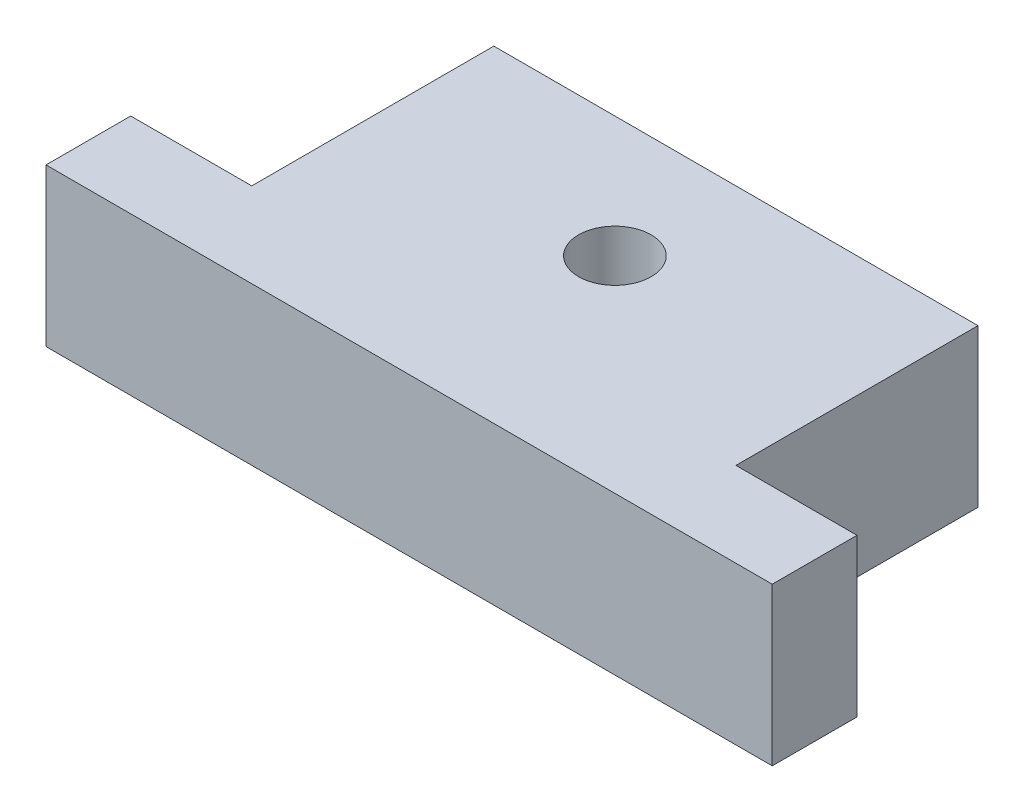
SolidWorks part; units mm, degrees
ref_plane "Front Plane" through (0, 0, 0) normal (0, 0, 1) x (1, 0, 0)
ref_plane "Top Plane" through (0, 0, 0) normal (0, 1, 0) x (1, 0, 0)
ref_plane "Right Plane" through (0, 0, 0) normal (1, 0, 0) x (0, 0, -1)
sketch "Sketch1" plane through (0, 0, 0) normal (0, 1, 0) x (1, 0, 0)
  line L0 (-23.4364, 11.7908) -> (36.5636, 11.7908)
  line L1 (36.5636, 11.7908) -> (36.5636, 18.7908)
  line L2 (36.5636, 18.7908) -> (26.5636, 18.7908)
  line L3 (26.5636, 18.7908) -> (26.5636, 38.7908)
  line L4 (26.5636, 38.7908) -> (-13.4364, 38.7908)
  line L5 (-13.4364, 38.7908) -> (-13.4364, 18.7908)
  line L6 (-13.4364, 18.7908) -> (-23.4364, 18.7908)
  line L7 (-23.4364, 18.7908) -> (-23.4364, 11.7908)
  line L8 (6.5636, 38.7908) -> (6.5636, 1.2081) construction
  line L9 (-13.4364, 28.7908) -> (26.5636, 28.7908) construction
  circle A0 centre (6.5636, 28.7908) radius 3
  dimension "D1" = 60
  dimension "D2" = 10
  dimension "40" = 40
  dimension "D3" = 7
  dimension "D4" = 7
  dimension "D5" = 20
  dimension "D6" = 20
extrude "Boss-Extrude1" add sketch "Sketch1" along normal blind 13
sketch "Sketch2" plane through (0, 0, -11.7908) normal (0, 0, 1) x (1, 0, 0)
  line L0 (6.5636, 13) -> (6.5636, 0)
  line L1 (-23.4364, 13) -> (36.5636, 13) construction
  line L2 (-23.4364, 0) -> (36.5636, 0) construction
